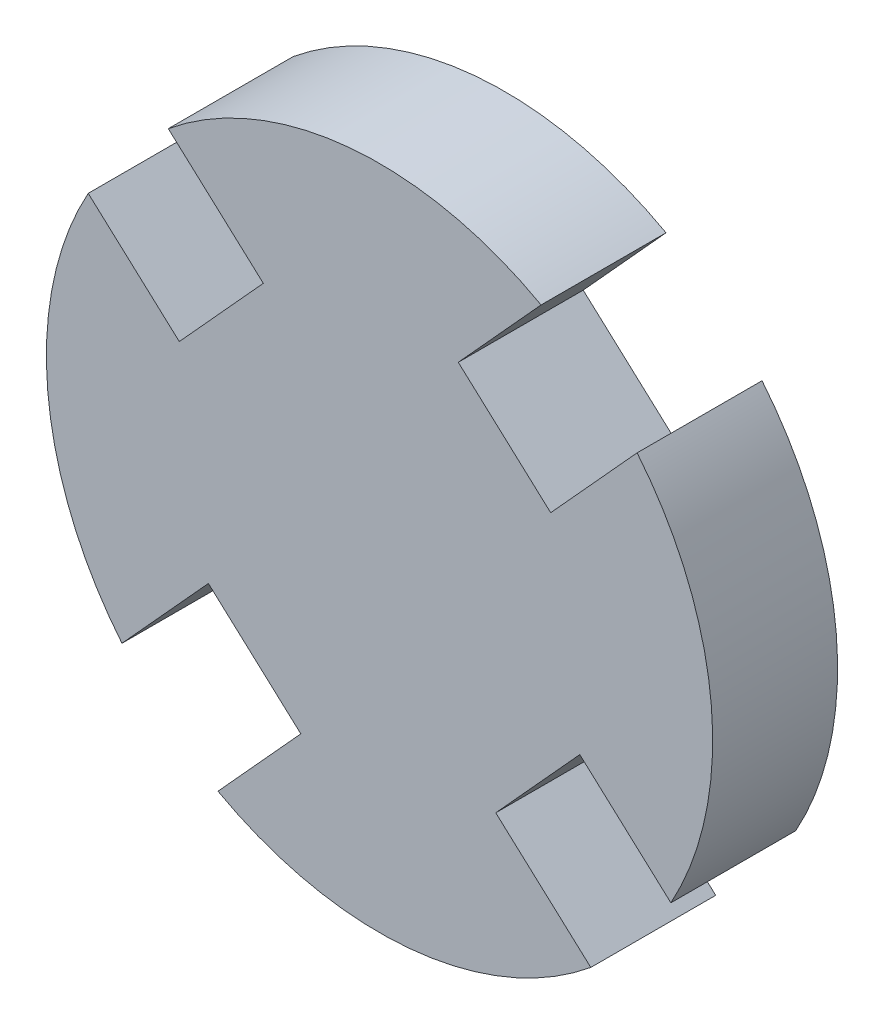
SolidWorks part; units mm, degrees
ref_plane "Alzado" through (0, 0, 0) normal (0, 0, 1) x (1, 0, 0)
ref_plane "Planta" through (0, 0, 0) normal (0, 1, 0) x (1, 0, 0)
ref_plane "Vista lateral" through (0, 0, 0) normal (1, 0, 0) x (0, 0, -1)
sketch "Croquis3" plane through (0, 0, 0) normal (0, 0, 1) x (1, 0, 0)
  line L1 (-1.8907, -4.8089) -> (-5.2542, -8.5084)
  line L3 (2.7908, -4.1104) -> (6.5658, -7.5426)
  line L4 (-4.1104, -2.7908) -> (-7.5426, -6.5658)
  line L5 (4.8089, -1.8907) -> (8.5084, -5.2542)
  line L6 (4.8089, -1.8907) -> (2.7908, -4.1104)
  line L7 (-1.8907, -4.8089) -> (-4.1104, -2.7908)
  line L8 (-4.8089, 1.8907) -> (-8.5084, 5.2542)
  line L9 (-2.7908, 4.1104) -> (-6.5658, 7.5426)
  line L10 (-4.8089, 1.8907) -> (-2.7908, 4.1104)
  line L11 (1.8907, 4.8089) -> (5.2542, 8.5084)
  line L12 (4.1104, 2.7908) -> (7.5426, 6.5658)
  line L13 (1.8907, 4.8089) -> (4.1104, 2.7908)
  arc A0 (-8.5084, 5.2542) -> (-7.5426, -6.5658) centre (0, 0) ccw
  arc A1 (5.2542, 8.5084) -> (-6.5658, 7.5426) centre (0, 0) ccw
  arc A2 (8.5084, -5.2542) -> (7.5426, 6.5658) centre (0, 0) ccw
  arc A3 (-5.2542, -8.5084) -> (6.5658, -7.5426) centre (0, 0) ccw
  point P1 (0.8144, -9.9668)
  point P11 (0, 10)
  point P24 (0, 0)
extrude "Saliente-Extruir3" add sketch "Croquis3" along normal blind 3 separate body contours L9 A1 L11 L13 L12 A2 L5 L6 L3 A3 L1 L7 L4 A0 L8 L10
sketch "Croquis4" plane through (0, 0, 3) normal (0, 0, 1) x (1, 0, 0)
  circle A0 centre (0, 0) radius 8
  circle A1 centre (0, 0) radius 10
extrude "Cortar-Extruir4" cut sketch "Croquis4" against normal through all contours A1 | A0
equation "\"Original Radius\"= 10mm"
equation "\"Material thickness\"= 3mm"
equation "\"Cut depth\"= 5mm"
equation "\"Distance between cuts\"= 11.82mm"
equation "\"Final radius\"= 8mm"
equation "\"D5@Croquis3\"=\"Distance between cuts\""
equation "\"D2@Croquis3\"=\"Cut depth\""
equation "\"D4@Croquis3\"=\"Material thickness\""
equation "\"D1@Croquis3\"=\"Original Radius\""
equation "\"D2@Croquis4\"=\"Original Radius\""
equation "\"D1@Croquis4\"=\"Final radius\""
equation "\"Distance from cut to origin\"= 4.83mm"
equation "\"D6@Croquis3\"=\"Distance from cut to origin\""
